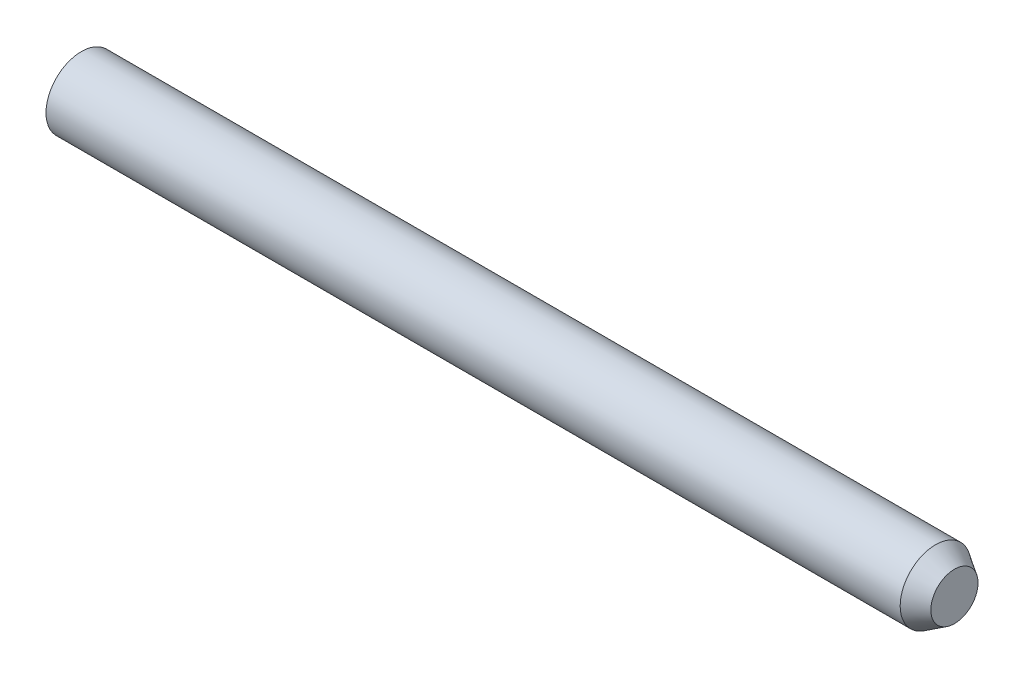
SolidWorks part; units mm, degrees
ref_plane "Front Plane" through (0, 0, 0) normal (0, 0, 1) x (1, 0, 0)
ref_plane "Top Plane" through (0, 0, 0) normal (0, 1, 0) x (1, 0, 0)
ref_plane "Right Plane" through (0, 0, 0) normal (1, 0, 0) x (0, 0, -1)
sketch "Sketch2" plane through (0, 0, 0) normal (0, 0, 1) x (1, 0, 0)
  line L1 (-65, -10) -> (-65, -15)
  line L2 (-65, -15) -> (255, -15)
  line L4 (255, -15) -> (297, -15)
  line L5 (297, -15) -> (305, -10)
  line L6 (255, -15) -> (65, -15)
  line L8 (-65, -10) -> (65, -10)
  line L9 (65, -10) -> (305, -10)
  line L11 (-65, 0) -> (305, 0)
  line L12 (305, -10) -> (305, 0)
  line L13 (293.5539, -10) -> (293.5539, 0)
  point P4 (0, 0)
  dimension "D1" = 320
  dimension "D2" = 5
  dimension "D3" = 50
  dimension "D4" = 15
  dimension "D5" = 5
revolve "Revolve2" add sketch "Sketch2" angle 360 about L11
